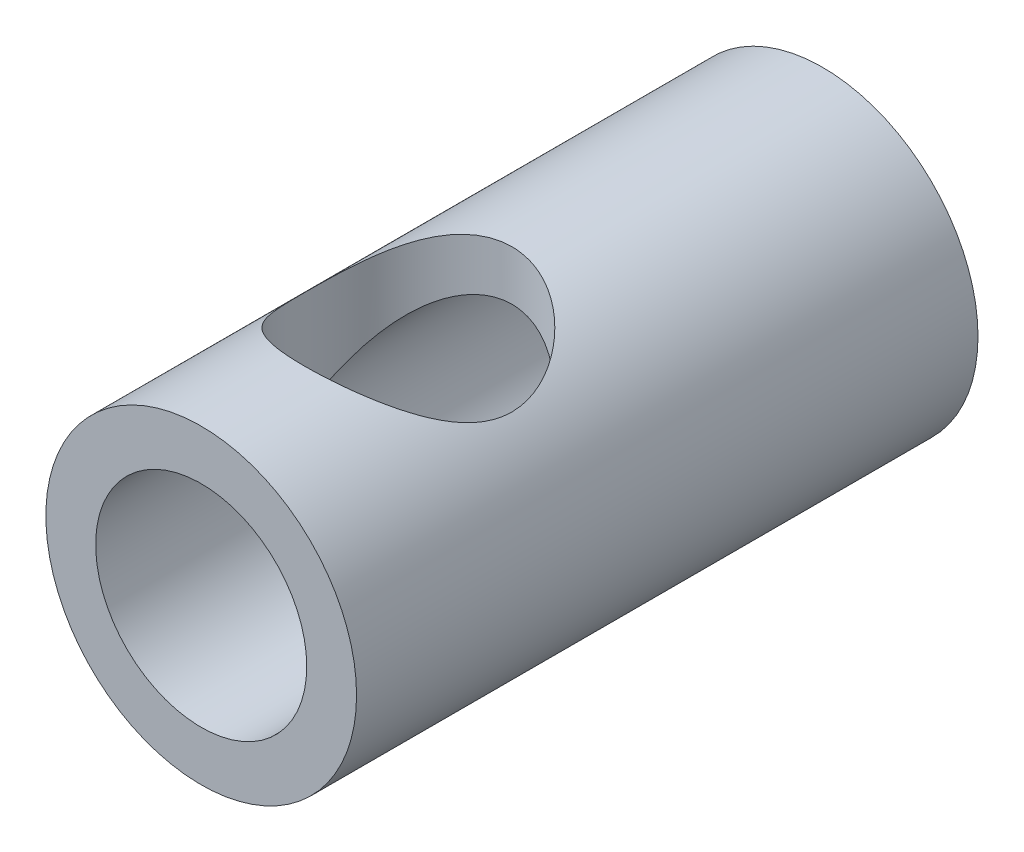
SolidWorks part; units mm, degrees
ref_plane "Front Plane" through (0, 0, 0) normal (0, 0, 1) x (1, 0, 0)
ref_plane "Top Plane" through (0, 0, 0) normal (0, 1, 0) x (1, 0, 0)
ref_plane "Right Plane" through (0, 0, 0) normal (1, 0, 0) x (0, 0, -1)
sketch "Sketch1" plane through (0, 0, 0) normal (0, 0, 1) x (1, 0, 0)
  circle A0 centre (0, 0) radius 2.0381
  circle A1 centre (0, 0) radius 3
  dimension "D1" = 4.0762
  dimension "D2" = 6
extrude "Boss-Extrude1" add sketch "Sketch1" along normal blind 12
sketch "Sketch2" plane through (0, 0, 0) normal (0, 1, 0) x (1, 0, 0)
  circle A0 centre (0, -8) radius 2
  dimension "D1" = 4
  dimension "D2" = 8
extrude "Cut-Extrude1" cut sketch "Sketch2" along normal through all
